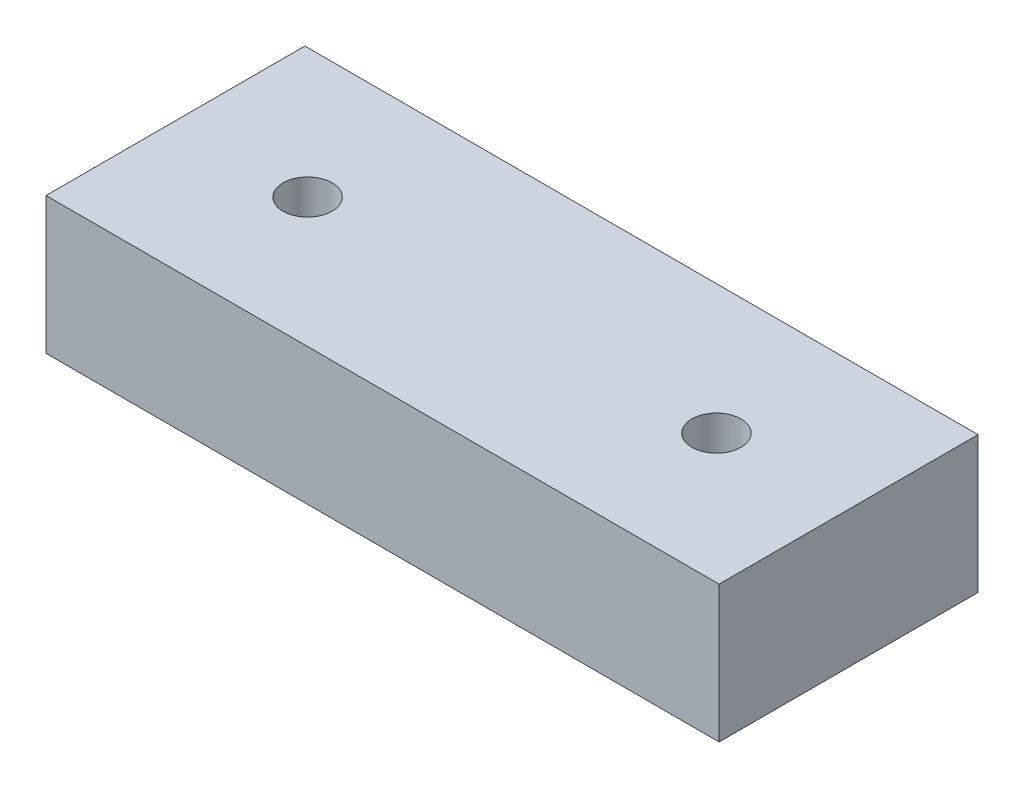
SolidWorks part; units mm, degrees
ref_plane "Front Plane" through (0, 0, 0) normal (0, 0, 1) x (1, 0, 0)
ref_plane "Top Plane" through (0, 0, 0) normal (0, 1, 0) x (1, 0, 0)
ref_plane "Right Plane" through (0, 0, 0) normal (1, 0, 0) x (0, 0, -1)
sketch "Sketch1" plane through (0, 0, 0) normal (0, 1, 0) x (1, 0, 0)
  line L1 (15.4781, -5.9531) -> (-15.4781, -5.9531)
  line L2 (15.4781, -5.9531) -> (15.4781, 5.9531)
  line L3 (15.4781, 5.9531) -> (-15.4781, 5.9531)
  line L4 (-15.4781, -5.9531) -> (-15.4781, 5.9531)
  line L5 (15.4781, -5.9531) -> (-15.4781, 5.9531) construction
  line L6 (15.4781, 5.9531) -> (-15.4781, -5.9531) construction
  point P0 (0, 0)
  dimension "D1" = 30.9562
  dimension "D2" = 11.9062
extrude "Boss-Extrude1" add sketch "Sketch1" along normal blind 6.2865
sketch "Sketch2" plane through (0, 0, 0) normal (0, -1, 0) x (1, 0, 0)
  circle A0 centre (0, 0) radius 2.3813
  dimension "D1" = 4.7625
extrude "Cut-Extrude1" cut sketch "Sketch2" against normal blind 4.7625
hole_wizard "#4-40 Tapped Hole1" positions "Sketch4" profile "Sketch3" tap size "#4-40" standard "Ansi Inch"
sketch "Sketch4" plane through (0, 6.2865, 0) normal (0, 1, 0) x (-1, 0, 0)
  line L0 (0, 0) -> (0, -4.4557) construction
  point P0 (9.402, 0)
  point P8 (-9.402, 0)
sketch "Sketch3" plane through (-9.402, 6.2865, 0) normal (1, 0, 0) x (0, 0, 1)
  line L0 (0, 0) -> (0, 9.5692)
  line L1 (0, 9.5692) -> (1.1303, 8.89)
  line L2 (1.1303, 8.89) -> (1.1303, 0)
  line L5 (1.1303, 0) -> (0, 0)
  line L10 (0, 9.5692) -> (-1.1303, 8.89) construction
  line L11 (0, -6.35) -> (0, 107.95) construction
  dimension "Tap Drill Dia." = 2.2606
  dimension "Tap Drill Depth" = 8.89
  dimension "Drill Angle" = 118
cosmetic thread "Hole Thread1" parameters "D1"=5.588, "D2"=2.8448
cosmetic thread "Hole Thread2" parameters "D1"=5.588, "D2"=2.8448
